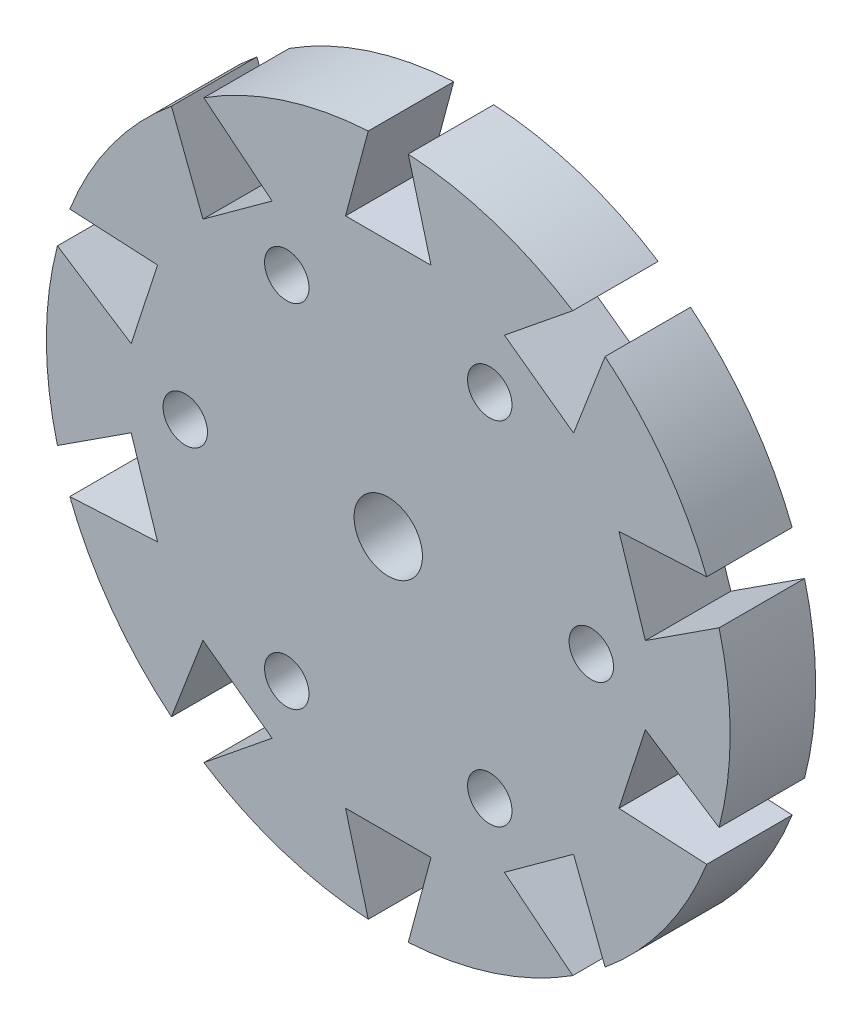
SolidWorks part; units mm, degrees
material "Acrylic (Medium-high impact)"
ref_plane "Front Plane" through (0, 0, 0) normal (0, 0, 1) x (1, 0, 0)
ref_plane "Top Plane" through (0, 0, 0) normal (0, 1, 0) x (1, 0, 0)
ref_plane "Right Plane" through (0, 0, 0) normal (1, 0, 0) x (0, 0, -1)
sketch "Sketch1" plane through (0, 0, 0) normal (0, 0, 1) x (1, 0, 0)
  circle A0 centre (0, 0) radius 40
  circle A1 centre (0, 0) radius 4
  circle A3 centre (-23.75, 0) radius 2.6
  circle A4 centre (-11.875, 20.5681) radius 2.6
  circle A5 centre (11.875, 20.5681) radius 2.6
  circle A6 centre (23.75, 0) radius 2.6
  circle A7 centre (11.875, -20.5681) radius 2.6
  circle A8 centre (-11.875, -20.5681) radius 2.6
  point P4 (0, 0)
  point P19 (0, 0)
  dimension "D1" = 80
  dimension "D2" = 8
  dimension "D3" = 23.75
  dimension "D5" = 5.2
  dimension "D6" = 23.75
  dimension "D4" = 6
  dimension "D7" = 20.5681
extrude "Boss-Extrude1" add sketch "Sketch1" along normal blind 10
sketch "Sketch3" plane through (0, 0, 10) normal (0, 0, 1) x (1, 0, 0)
  line L0 (-2.3388, 39.9316) -> (-5, 30)
  line L1 (-5, 30) -> (5, 30)
  line L2 (5, 30) -> (2.3388, 39.9316)
  line L3 (0, 0) -> (0, 40) construction
  circle A0 centre (0, 0) radius 40 construction
  dimension "D1" = 10
  dimension "D2" = 75
  dimension "D3" = 10
extrude "Cut-Extrude1" cut sketch "Sketch3" against normal through all both and the other way through all
pattern_circular "CirPattern1" count 10 over 360 about axis through (0, 0, 10) along (0, 0, 1) of "Cut-Extrude1"
